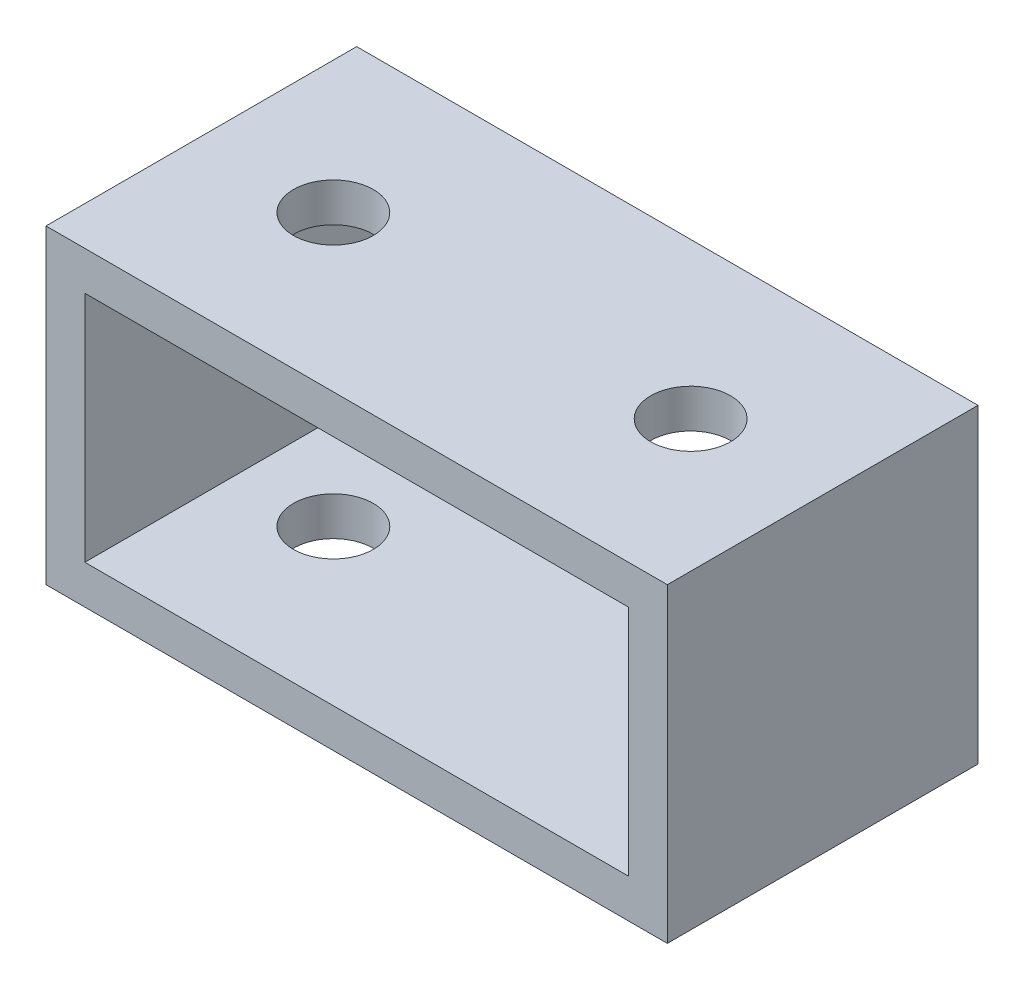
SolidWorks part; units mm, degrees
ref_plane "Front Plane" through (0, 0, 0) normal (0, 0, 1) x (1, 0, 0)
ref_plane "Top Plane" through (0, 0, 0) normal (0, 1, 0) x (1, 0, 0)
ref_plane "Right Plane" through (0, 0, 0) normal (1, 0, 0) x (0, 0, -1)
sketch "Sketch1" plane through (0, 0, 0) normal (0, 0, 1) x (1, 0, 0)
  line L0 (3.175, 3.175) -> (3.175, 22.225)
  line L1 (0, 0) -> (50.8, 0)
  line L2 (0, 0) -> (0, 25.4)
  line L3 (0, 25.4) -> (50.8, 25.4)
  line L4 (50.8, 0) -> (50.8, 25.4)
  line L5 (3.175, 22.225) -> (47.625, 22.225)
  line L6 (47.625, 3.175) -> (47.625, 22.225)
  line L7 (3.175, 3.175) -> (47.625, 3.175)
  dimension "D1" = 25.4
  dimension "D2" = 50.8
  dimension "D3" = 3.175
extrude "Boss-Extrude1" add sketch "Sketch1" along normal blind 25.4
sketch "Sketch8" plane through (0, 25.4, 0) normal (0, 1, 0) x (1, 0, 0)
  line L1 (10.795, -12.7) -> (40.005, -12.7) construction
  line L2 (25.4, 0) -> (25.4, -25.4) construction
  line L3 (50.8, 0) -> (0, 0) construction
  line L4 (50.8, -25.4) -> (0, -25.4) construction
  circle A0 centre (10.795, -12.7) radius 3.2639
  circle A1 centre (40.005, -12.7) radius 3.2639
  point P10 (25.4, -12.7)
  point P11 (9.9867, -12.7)
  dimension "D2" = 6.5278
  dimension "D1" = 12.7
  dimension "D3" = 29.21
extrude "Cut-Extrude1" cut sketch "Sketch8" against normal through all both and the other way through all
